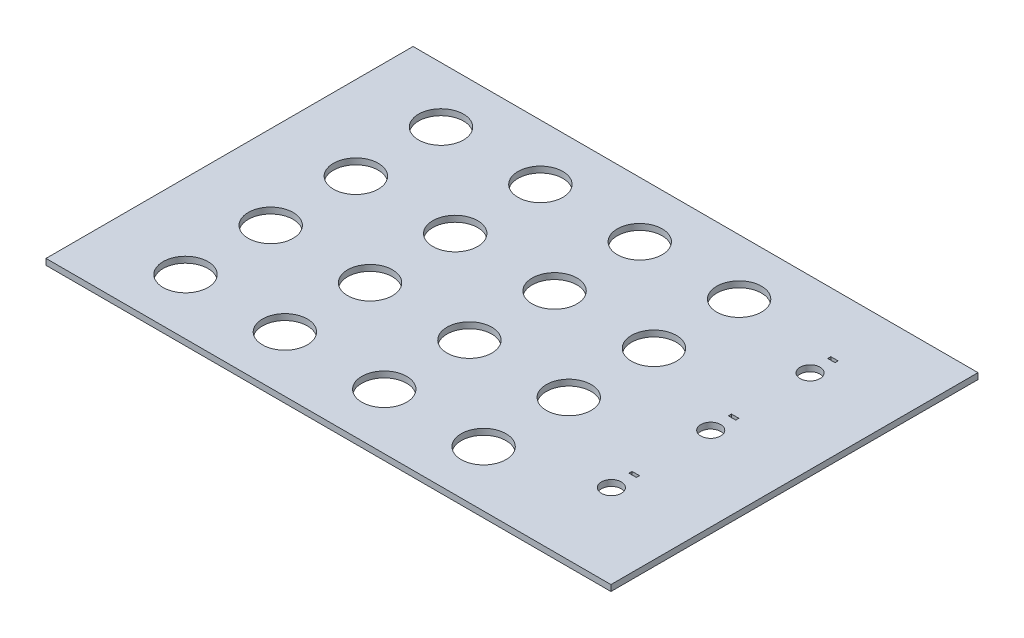
SolidWorks part; units mm, degrees
ref_plane "Front Plane" through (0, 0, 0) normal (0, 0, 1) x (1, 0, 0)
ref_plane "Top Plane" through (0, 0, 0) normal (0, 1, 0) x (1, 0, 0)
ref_plane "Right Plane" through (0, 0, 0) normal (1, 0, 0) x (0, 0, -1)
sketch "Sketch1" plane through (0, 0, 0) normal (0, 1, 0) x (1, 0, 0)
  line L0 (-70, 86.9805) -> (-70, -106.8016) construction
  line L1 (99.5, 64.65) -> (-99.5, 64.65)
  line L2 (99.5, 64.65) -> (99.5, -64.65)
  line L3 (99.5, -64.65) -> (-99.5, -64.65)
  line L4 (-99.5, 64.65) -> (-99.5, -64.65)
  line L5 (99.5, 64.65) -> (-99.5, -64.65) construction
  line L6 (99.5, -64.65) -> (-99.5, 64.65) construction
  line L7 (0, 64.65) -> (0, -64.65) construction
  line L8 (-99.5, 0) -> (99.5, 0) construction
  line L9 (-70, 45) -> (-35, 45) construction
  line L10 (60.6732, 35) -> (77.1303, 35) construction
  line L11 (68.7, 43.6) -> (71.3, 43.6)
  line L12 (68.7, 43.6) -> (68.7, 42.5)
  line L13 (68.7, 42.5) -> (71.3, 42.5)
  line L14 (71.3, 43.6) -> (71.3, 42.5)
  line L15 (68.7, 43.6) -> (71.3, 42.5) construction
  line L16 (68.7, 42.5) -> (71.3, 43.6) construction
  line L17 (68.7, 8.6) -> (68.7, 7.5)
  line L18 (68.7, 8.6) -> (71.3, 8.6)
  line L19 (71.3, 8.6) -> (71.3, 7.5)
  line L20 (68.7, 7.5) -> (71.3, 7.5)
  line L21 (68.7, -26.4) -> (68.7, -27.5)
  line L22 (68.7, -26.4) -> (71.3, -26.4)
  line L23 (71.3, -26.4) -> (71.3, -27.5)
  line L24 (68.7, -27.5) -> (71.3, -27.5)
  circle A0 centre (-70, 45) radius 7.9
  circle A1 centre (-35, 45) radius 7.9
  circle A2 centre (0, 45) radius 7.9
  circle A3 centre (35, 45) radius 7.9
  circle A4 centre (-35, 15) radius 7.9
  circle A5 centre (0, 15) radius 7.9
  circle A6 centre (35, 15) radius 7.9
  circle A7 centre (-35, -15) radius 7.9
  circle A8 centre (0, -15) radius 7.9
  circle A9 centre (35, -15) radius 7.9
  circle A10 centre (-35, -45) radius 7.9
  circle A11 centre (0, -45) radius 7.9
  circle A12 centre (35, -45) radius 7.9
  circle A13 centre (-70, 15) radius 7.9
  circle A14 centre (-70, -15) radius 7.9
  circle A15 centre (-70, -45) radius 7.9
  circle A16 centre (70, 35) radius 3.5
  circle A17 centre (70, 0) radius 3.5
  circle A18 centre (70, -35) radius 3.5
  point P0 (0, 0)
  point P14 (70, 43.05)
  dimension "D3" = 15.8
  dimension "D15" = 7
  dimension "D19" = 3
  dimension "D1" = 129.3
  dimension "D2" = 199
  dimension "D4" = 4
  dimension "D6" = 35
  dimension "D7" = 19.65
  dimension "D8" = 19.65
  dimension "D9" = 3
  dimension "D10" = 29.65
  dimension "D11" = 29.65
  dimension "D12" = 35
  dimension "D13" = 29.5
  dimension "D14" = 29.5
  dimension "D16" = 2.6
  dimension "D17" = 7.5
  dimension "D18" = 1.1
  dimension "D20" = 7.5
  dimension "D5" = 4
extrude "Boss-Extrude1" add sketch "Sketch1" along normal blind 2.13
